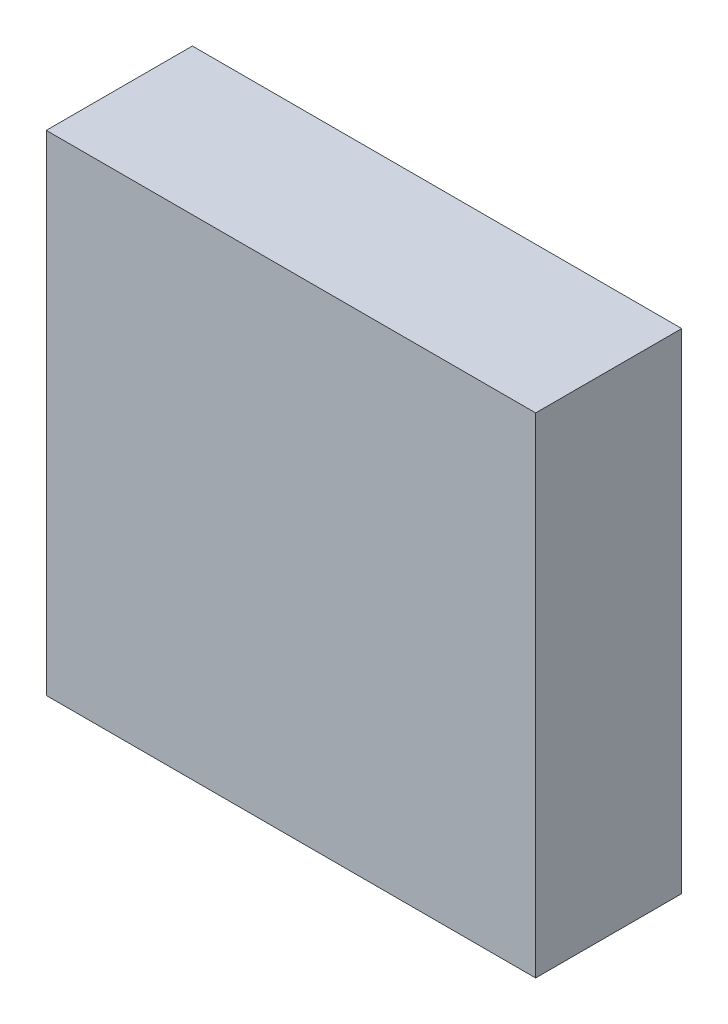
SolidWorks part; units mm, degrees
ref_plane "Piano frontale" through (0, 0, 0) normal (0, 0, 1) x (1, 0, 0)
ref_plane "Piano superiore" through (0, 0, 0) normal (0, 1, 0) x (1, 0, 0)
ref_plane "Piano destro" through (0, 0, 0) normal (1, 0, 0) x (0, 0, -1)
sketch "Schizzo1" plane through (0, 0, 0) normal (0, 0, 1) x (1, 0, 0)
  line L1 (0, 0) -> (41.2, 0)
  line L2 (0, 0) -> (0, 41.2)
  line L3 (0, 41.2) -> (41.2, 41.2)
  line L4 (41.2, 0) -> (41.2, 41.2)
  dimension "D1" = 41.2
  dimension "D2" = 41.2
extrude "Estrusione-Estrusione1" add sketch "Schizzo1" along normal blind 12.3
sketch "Schizzo2" plane through (0, 41.2, 0) normal (0, 1, 0) x (1, 0, 0)
  line L4 (2.2, -5.1) -> (8.8, -5.1)
  line L5 (2.2, -5.1) -> (2.2, -1.6)
  line L6 (2.2, -1.6) -> (8.8, -1.6)
  line L7 (8.8, -5.1) -> (8.8, -1.6)
  dimension "D3" = 3.5
  dimension "D4" = 6.6
extrude "Taglio-Estrusione1" cut sketch "Schizzo2" against normal blind 42
sketch "Schizzo3" plane through (0, 0, 5.1) normal (0, 0, -1) x (-1, 0, 0)
  line L0 (-2.2, 0) -> (-2.2, 41.2) construction
  line L1 (-8.8, 41.2) -> (-2.2, 41.2)
  line L2 (-8.8, 41.2) -> (-8.8, 38.9386)
  line L3 (-8.8, 38.9386) -> (-2.2, 38.9386)
  line L4 (-2.2, 41.2) -> (-2.2, 38.9386)
extrude "Estrusione-Estrusione2" add sketch "Schizzo3" along normal blind 5
